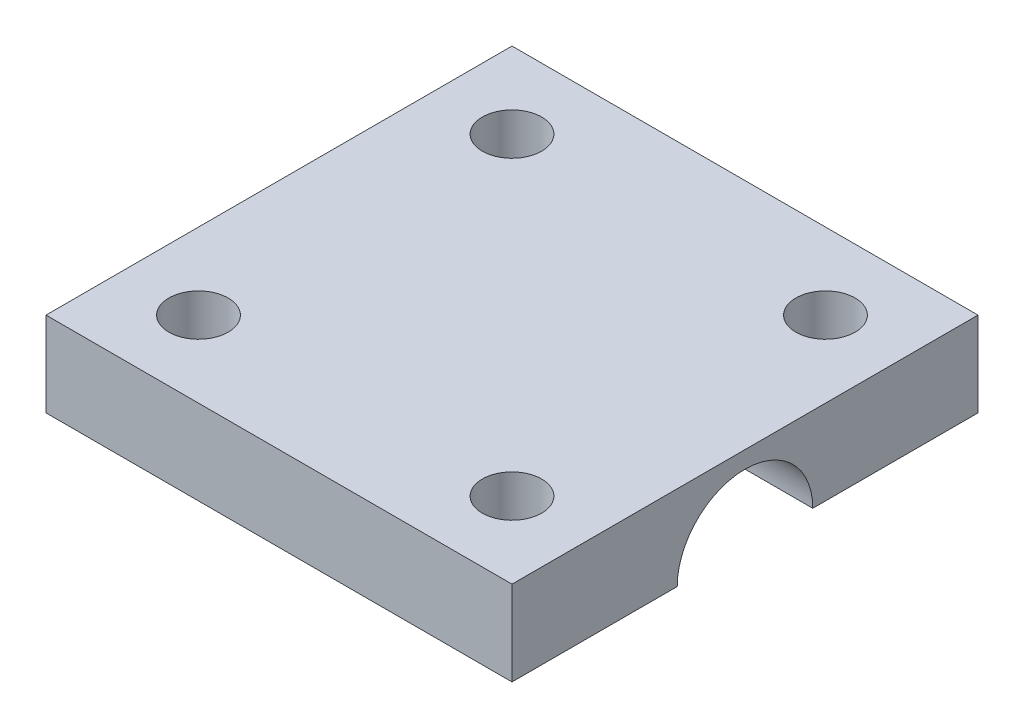
SolidWorks part; units mm, degrees
material "5052-H34"
ref_plane "Front Plane" through (0, 0, 0) normal (0, 0, 1) x (1, 0, 0)
ref_plane "Top Plane" through (0, 0, 0) normal (0, 1, 0) x (1, 0, 0)
ref_plane "Right Plane" through (0, 0, 0) normal (1, 0, 0) x (0, 0, -1)
sketch "Sketch1" plane through (0, 0, 0) normal (0, 1, 0) x (1, 0, 0)
  line L1 (-27.5, 27.5) -> (27.5, 27.5)
  line L2 (-27.5, 27.5) -> (-27.5, -27.5)
  line L3 (-27.5, -27.5) -> (27.5, -27.5)
  line L4 (27.5, 27.5) -> (27.5, -27.5)
  line L5 (-27.5, 27.5) -> (27.5, -27.5) construction
  line L6 (-27.5, -27.5) -> (27.5, 27.5) construction
  point P0 (0, 0)
  dimension "D1" = 55
  dimension "D2" = 55
extrude "Boss-Extrude1" add sketch "Sketch1" along normal blind 10
sketch "Sketch2" plane through (27.5, 0, 0) normal (1, 0, 0) x (0, 0, -1)
  circle A0 centre (0, 0) radius 8
  dimension "D1" = 16
extrude "Cut-Extrude1" cut sketch "Sketch2" against normal blind 50
sketch "Sketch3" plane through (0, 10, 0) normal (0, 1, 0) x (1, 0, 0)
  line L0 (27.5, 27.5) -> (-27.5, 27.5) construction
  line L1 (-18.5, 18.5) -> (18.5, 18.5) construction
  line L2 (-18.5, 18.5) -> (-18.5, -18.5) construction
  line L3 (-18.5, -18.5) -> (18.5, -18.5) construction
  line L4 (18.5, 18.5) -> (18.5, -18.5) construction
  line L5 (-18.5, 18.5) -> (18.5, -18.5) construction
  line L6 (-18.5, -18.5) -> (18.5, 18.5) construction
  line L7 (27.5, -27.5) -> (27.5, 27.5) construction
  circle A0 centre (-18.5, 18.5) radius 3.5
  circle A1 centre (18.5, 18.5) radius 3.5
  circle A2 centre (-18.5, -18.5) radius 3.5
  circle A3 centre (18.5, -18.5) radius 3.5
  point P0 (0, 0)
  dimension "D3" = 7
  dimension "D1" = 9
  dimension "D2" = 9
extrude "Cut-Extrude2" cut sketch "Sketch3" against normal blind 50
cosmetic thread "Cosmetic Thread1" parameters "D2"=10
cosmetic thread "Cosmetic Thread2" parameters "D2"=10
cosmetic thread "Cosmetic Thread3" parameters "D2"=10
cosmetic thread "Cosmetic Thread4" parameters "D2"=10
